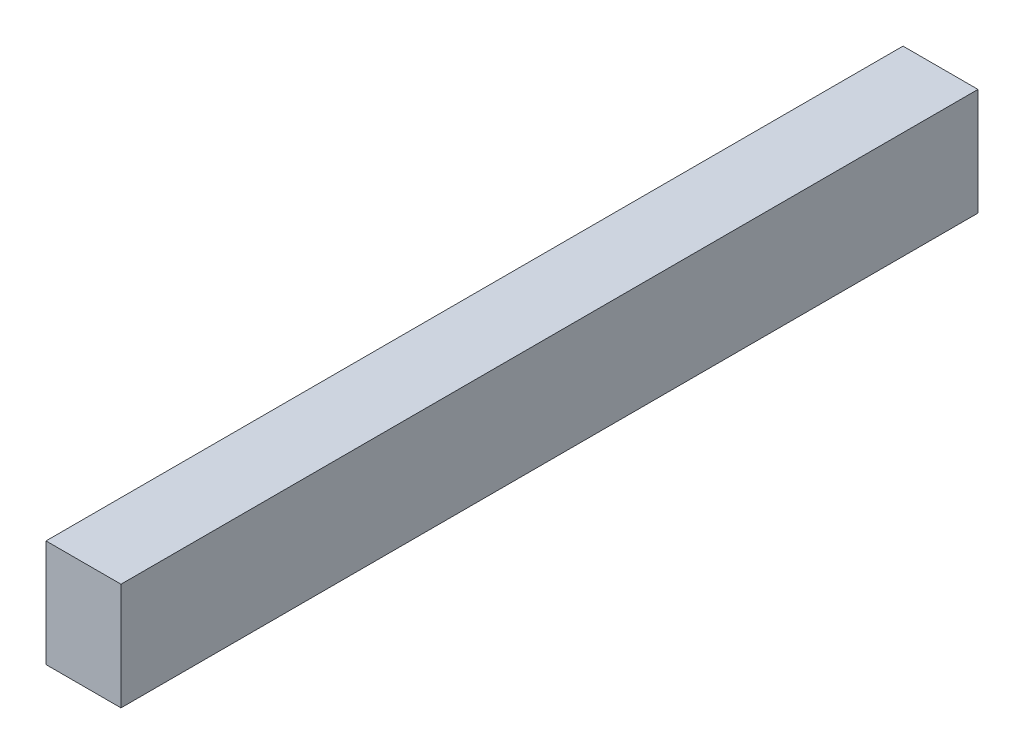
SolidWorks part; units mm, degrees
ref_plane "Front Plane" through (0, 0, 0) normal (0, 0, 1) x (1, 0, 0)
ref_plane "Top Plane" through (0, 0, 0) normal (0, 1, 0) x (1, 0, 0)
ref_plane "Right Plane" through (0, 0, 0) normal (1, 0, 0) x (0, 0, -1)
sketch "Sketch1" plane through (0, 0, 0) normal (0, 0, 1) x (1, 0, 0)
  line L1 (0, 0) -> (7, 0)
  line L2 (0, 0) -> (0, 10)
  line L3 (0, 10) -> (7, 10)
  line L4 (7, 0) -> (7, 10)
  dimension "D1" = 10
  dimension "D2" = 7
extrude "Boss-Extrude1" add sketch "Sketch1" along normal blind 80
